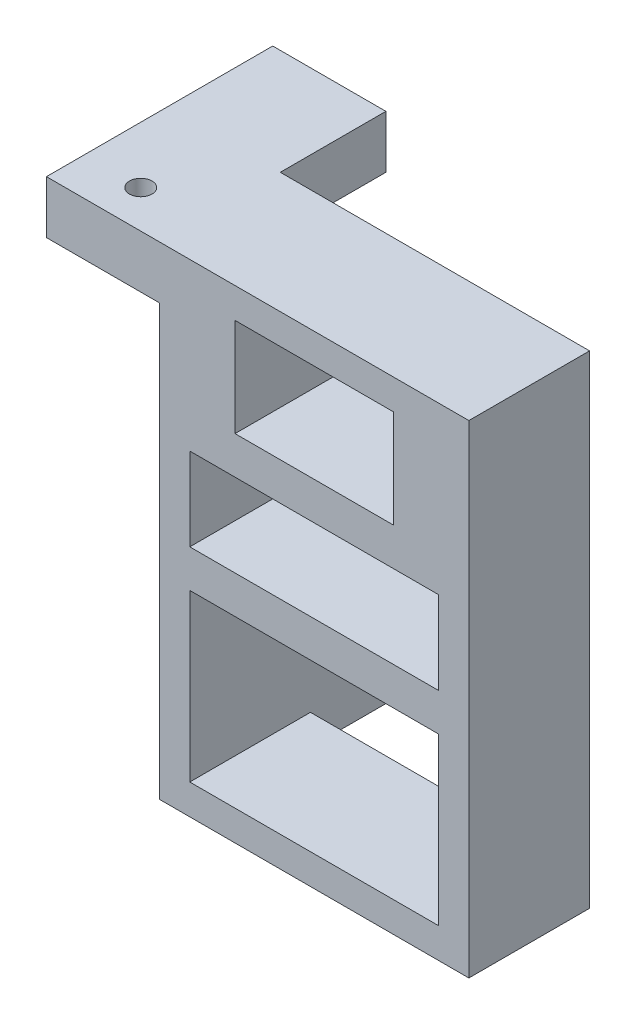
SolidWorks part; units mm, degrees
ref_plane "Alzado" through (0, 0, 0) normal (0, 0, 1) x (1, 0, 0)
ref_plane "Planta" through (0, 0, 0) normal (0, 1, 0) x (1, 0, 0)
ref_plane "Vista lateral" through (0, 0, 0) normal (1, 0, 0) x (0, 0, -1)
sketch "Croquis1" plane through (0, 0, 0) normal (0, 0, 1) x (1, 0, 0)
  line L1 (-103.4942, 44.0278) -> (-62.4942, 44.0278)
  line L2 (-103.4942, 44.0278) -> (-103.4942, -19.9722)
  line L3 (-103.4942, -19.9722) -> (-62.4942, -19.9722)
  line L4 (-62.4942, 44.0278) -> (-62.4942, -19.9722)
  line L5 (-99.4942, 6.0278) -> (-66.4942, 6.0278)
  line L6 (-99.4942, 6.0278) -> (-99.4942, -15.9722)
  line L7 (-99.4942, -15.9722) -> (-66.4942, -15.9722)
  line L8 (-66.4942, 6.0278) -> (-66.4942, -15.9722)
  line L9 (-99.4942, 11.0278) -> (-66.4942, 11.0278)
  line L10 (-99.4942, 11.0278) -> (-99.4942, 22.0278)
  line L11 (-99.4942, 22.0278) -> (-66.4942, 22.0278)
  line L12 (-66.4942, 11.0278) -> (-66.4942, 22.0278)
  line L13 (-93.4942, 40.0278) -> (-72.4942, 40.0278)
  line L14 (-93.4942, 40.0278) -> (-93.4942, 27.0278)
  line L15 (-93.4942, 27.0278) -> (-72.4942, 27.0278)
  line L16 (-72.4942, 40.0278) -> (-72.4942, 27.0278)
  dimension "D1" = 64
  dimension "D2" = 41
  dimension "D3" = 33
  dimension "D4" = 4
  dimension "D5" = 22
  dimension "D6" = 4
  dimension "D7" = 5
  dimension "D8" = 11
  dimension "D9" = 5
  dimension "D10" = 21
  dimension "D11" = 10
  dimension "D12" = 13
extrude "Saliente-Extruir1" add sketch "Croquis1" along normal blind 16
sketch "Croquis2" plane through (-103.4942, 0, 0) normal (-1, 0, 0) x (0, 0, 1)
  line L1 (16, 44.0278) -> (16, -19.9722) construction
  line L2 (16, 37.0278) -> (-14, 37.0278)
  line L3 (16, 37.0278) -> (16, 44.0278)
  line L4 (16, 44.0278) -> (-14, 44.0278)
  line L7 (-14, 37.0278) -> (-14, 44.0278)
  line L8 (16, -19.9722) -> (0, -19.9722) construction
  dimension "D1" = 57
  dimension "D2" = 7
  dimension "D3" = 30
extrude "Saliente-Extruir2" add sketch "Croquis2" along normal blind 15
sketch "Croquis3" plane through (0, 0, 0) normal (0, 0, -1) x (-1, 0, 0)
  line L0 (103.4942, 37.0278) -> (103.4942, -19.9722) construction
  line L1 (103.4942, -19.9722) -> (99.4942, -19.9722)
  line L2 (103.4942, -19.9722) -> (103.4942, 6.0278)
  line L4 (99.4942, -19.9722) -> (99.4942, 6.0278)
  line L6 (99.4942, 6.0278) -> (99.4942, 16.0278)
  line L7 (99.4942, 16.0278) -> (103.4942, 16.0278)
  line L8 (103.4942, 6.0278) -> (103.4942, 16.0278)
  dimension "D1" = 10
extrude "Saliente-Extruir3" add sketch "Croquis3" along normal blind 22
sketch "Croquis4" plane through (-99.4942, 0, 0) normal (1, 0, 0) x (0, 0, -1)
  line L2 (22, 16.0278) -> (26, 16.0278)
  line L3 (22, 16.0278) -> (22, -19.9722)
  line L4 (22, -19.9722) -> (26, -19.9722)
  line L5 (26, 16.0278) -> (26, -19.9722)
  dimension "D1" = 4
extrude "Saliente-Extruir4" add sketch "Croquis4" against normal blind 19
sketch "Croquis5" plane through (0, 44.0278, 0) normal (0, 1, 0) x (1, 0, 0)
  line L0 (-118.4942, 14) -> (-103.4942, 14) construction
  line L1 (-103.4942, 0) -> (-103.4942, 14) construction
  circle A0 centre (-110.9942, -11) radius 1.5
  dimension "D1" = 25
  dimension "D2" = 7.5
extrude "Cortar-Extruir3" cut sketch "Croquis5" against normal up to vertex
sketch "Croquis7" plane through (0, 0, -22) normal (0, 0, 1) x (1, 0, 0)
  line L0 (-103.4942, -19.9722) -> (-103.4942, 16.0278) construction
  line L1 (-118.4942, -19.9722) -> (-103.4942, -19.9722) construction
  circle A0 centre (-110.9942, 5.0278) radius 1.5
  dimension "D1" = 7.5
  dimension "D2" = 25
extrude "Cortar-Extruir6" cut sketch "Croquis7" against normal up to vertex (4 mm away) up to point (-118.4942, -19.9722, -26)
